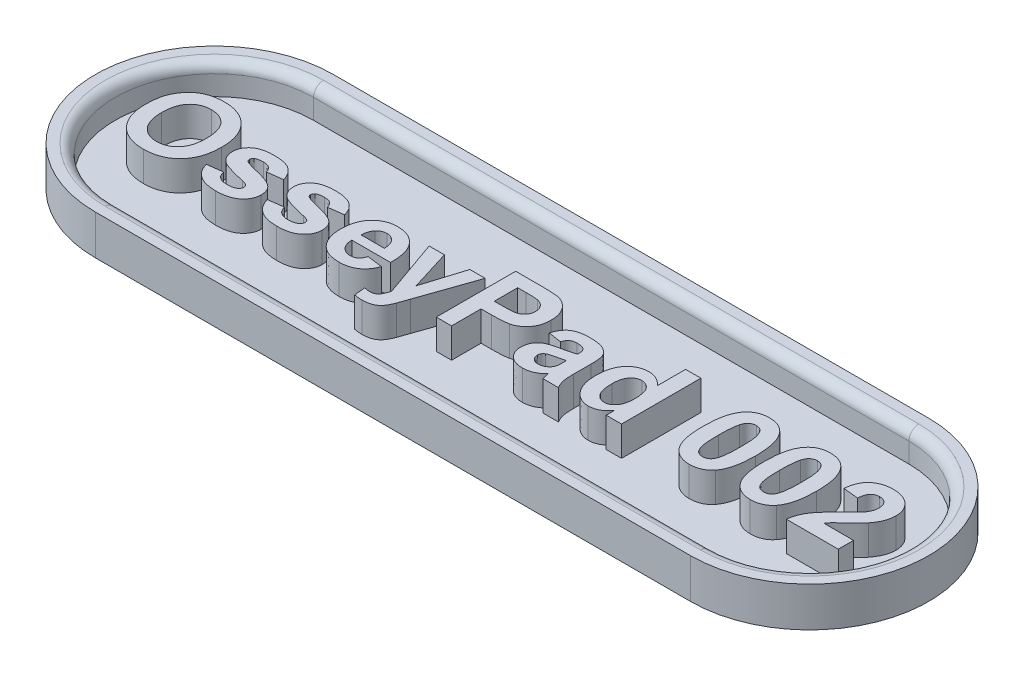
SolidWorks part; units mm, degrees
ref_plane "Front Plane" through (0, 0, 0) normal (0, 0, 1) x (1, 0, 0)
ref_plane "Top Plane" through (0, 0, 0) normal (0, 1, 0) x (1, 0, 0)
ref_plane "Right Plane" through (0, 0, 0) normal (1, 0, 0) x (0, 0, -1)
sketch "Sketch1" plane through (0, 0, 0) normal (0, 1, 0) x (1, 0, 0)
  line L0 (-15, 0) -> (15, 0) construction
  line L1 (-15, 6) -> (15, 6)
  line L2 (-15, -6) -> (15, -6)
  arc A0 (-15, 6) -> (-15, -6) centre (-15, 0) ccw
  arc A1 (15, -6) -> (15, 6) centre (15, 0) ccw
  point P2 (0, 0)
  dimension "D1" = 12
  dimension "D2" = 30
extrude "Boss-Extrude1" add sketch "Sketch1" along normal blind 2
sketch "Sketch2" plane through (0, 2, 0) normal (0, 1, 0) x (1, 0, 0)
  line L0 (-15, 0) -> (15, 0) construction
  line L1 (-15, 5) -> (15, 5)
  line L2 (-15, -5) -> (15, -5)
  arc A0 (-15, 5) -> (-15, -5) centre (-15, 0) ccw
  arc A1 (15, -5) -> (15, 5) centre (15, 0) ccw
  point P2 (0, 0)
  dimension "D1" = 30
  dimension "D2" = 10
extrude "Cut-Extrude1" cut sketch "Sketch2" against normal blind 1.5
sketch "Sketch3" plane through (0, 0.5, 0) normal (0, 1, 0) x (1, 0, 0)
  line L0 (-21, -1.995) -> (21, -1.995) construction
  line L1 (0, -8.7006) -> (0, 6.9821) construction
  line L3 (-15, -5) -> (15, -5) construction
  text T0 "OsseyPad 002" font "Arial" height 4
  dimension "D1" = 3.005
extrude "Boss-Extrude2" add sketch "Sketch3" along normal blind 1.5
fillet "Fillet1" radius 0.5 4 edges at (0, 2, -5) (20, 2, 0) (0, 2, 5) (-20, 2, 0)
